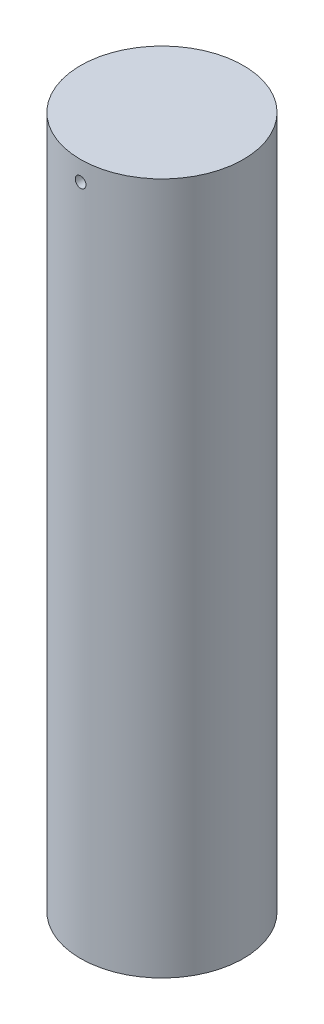
SolidWorks part; units mm, degrees
ref_plane "Front Plane" through (0, 0, 0) normal (0, 0, 1) x (1, 0, 0)
ref_plane "Top Plane" through (0, 0, 0) normal (0, 1, 0) x (1, 0, 0)
ref_plane "Right Plane" through (0, 0, 0) normal (1, 0, 0) x (0, 0, -1)
sketch "Sketch1" plane through (0, 0, 0) normal (0, 1, 0) x (1, 0, 0)
  circle A0 centre (0, 0) radius 6.35
  point P0 (0, 0)
extrude "Boss-Extrude1" add sketch "Sketch1" along normal blind 53.975
hole_wizard "1/4-20 Tapped Hole1" positions "Sketch4" profile "Sketch3" tap size "1/4-20" standard "ANSI Inch"
sketch "Sketch4" plane through (0, 0, 0) normal (0, -1, 0) x (-1, 0, 0)
  point P0 (0, 0)
sketch "Sketch3" plane through (0, 0, 0) normal (1, 0, 0) x (0, 0, -1)
  line L0 (0, 0) -> (0, 26.9338)
  line L1 (0, 26.9338) -> (2.5527, 25.4)
  line L2 (2.5527, 25.4) -> (2.5527, 0)
  line L5 (2.5527, 0) -> (0, 0)
  line L10 (0, 26.9338) -> (-2.5527, 25.4) construction
  line L11 (0, -6.35) -> (0, 107.95) construction
  dimension "Tap Drill Dia." = 5.1054
  dimension "Tap Drill Depth" = 25.4
  dimension "Drill Angle" = 118
cosmetic thread "Hole Thread1" parameters "D1"=25.4, "D2"=6.35
sketch "Sketch6" plane through (0, 0, 0) normal (0, -1, 0) x (-1, 0, 0)
  circle A0 centre (0, 0) radius 6.35 construction
  point P0 (0, -6.35)
ref_plane "Plane1" through (0, 0, 6.35) normal (0, 0, 1) x (1, 0, 0)
sketch "Sketch8" plane through (0, 0, 6.35) normal (0, 0, 1) x (1, 0, 0)
  line L0 (0, 0) -> (0, 52.07)
hole_wizard "#66 (0.033) Diameter Hole1" positions "3DSketch1" profile "Sketch9" hole size "#66" standard "ANSI Inch" end condition through all
sketch3d "3DSketch1"
  point P0 (-0.007, 52.4481, 6.35)
sketch "Sketch9" plane through (-0.007, 52.4481, 6.35) normal (0, 1, 0) x (1, 0, 0.0011)
  line L0 (0, 0) -> (0, 12.707)
  line L1 (0, 12.707) -> (0.4191, 12.707)
  line L2 (0.4191, 12.707) -> (0.4191, 0)
  line L5 (0.4191, 0) -> (0, 0)
  line L11 (0, -6.35) -> (0, 107.95) construction
  dimension "Thru Hole Dia." = 0.8382
  dimension "Thru Hole Depth" = 12.707
